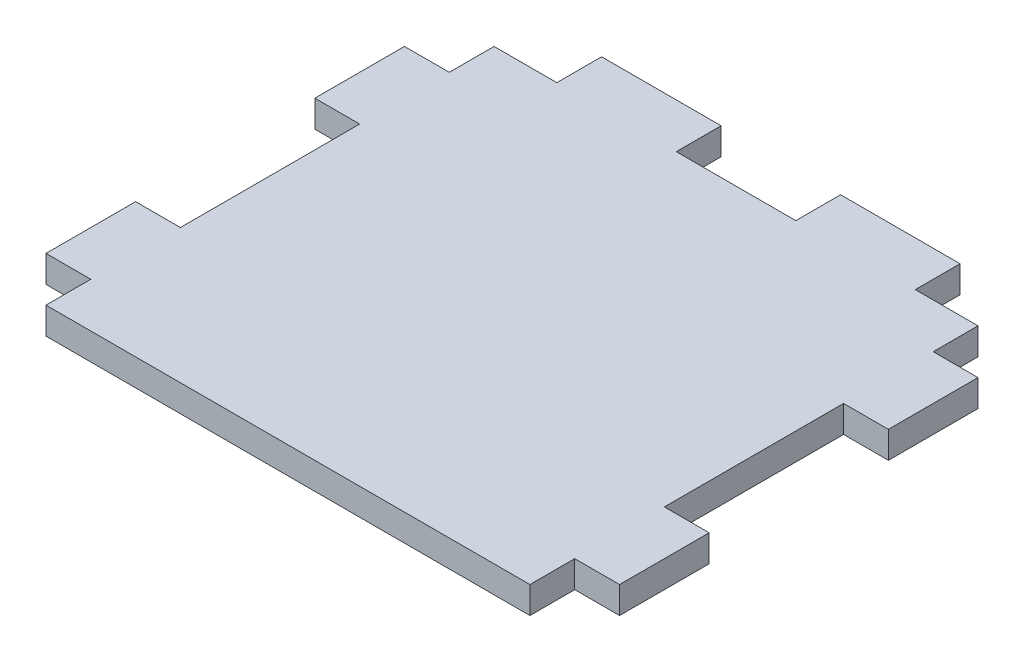
SolidWorks part; units mm, degrees
ref_plane "Front Plane" through (0, 0, 0) normal (0, 0, 1) x (1, 0, 0)
ref_plane "Top Plane" through (0, 0, 0) normal (0, 1, 0) x (1, 0, 0)
ref_plane "Right Plane" through (0, 0, 0) normal (1, 0, 0) x (0, 0, -1)
sketch "Sketch1" plane through (0, 0, 0) normal (0, 1, 0) x (1, 0, 0)
  line L0 (-45, 37.5) -> (-40.5, 37.5)
  line L1 (-45, 37.5) -> (-30, 37.5)
  line L3 (-45, -37.5) -> (45, -37.5)
  line L5 (-45, 37.5) -> (45, -37.5) construction
  line L6 (-45, -37.5) -> (45, 37.5) construction
  line L7 (45, 37.5) -> (40.5, 37.5)
  line L8 (-40.5, 37.5) -> (-40.5, 30)
  line L9 (-45, 37.5) -> (-30, 37.5)
  line L14 (-48, 30) -> (-40.5, 30)
  line L15 (-48, 30) -> (-48, 15)
  line L16 (-48, 15) -> (-40.5, 15)
  line L18 (-48, -30) -> (-48, -15)
  line L19 (-48, -30) -> (-40.5, -30)
  line L21 (-48, -15) -> (-40.5, -15)
  line L23 (48, 15) -> (40.5, 15)
  line L25 (48, 30) -> (40.5, 30)
  line L26 (48, 30) -> (48, 15)
  line L27 (48, -30) -> (40.5, -30)
  line L29 (48, -15) -> (40.5, -15)
  line L30 (48, -30) -> (48, -15)
  line L31 (-40.5, -30) -> (-40.5, -37.5)
  line L32 (40.5, 37.5) -> (40.5, 30)
  line L33 (-40.5, 15) -> (-40.5, -15)
  line L34 (40.5, 15) -> (40.5, -15)
  line L35 (-30, 45) -> (-10, 45)
  line L36 (40.5, -30) -> (40.5, -37.5)
  line L37 (-30, 45) -> (-30, 37.5)
  line L39 (-10, 45) -> (-10, 37.5)
  line L41 (10, 45) -> (10, 37.5)
  line L42 (30, 45) -> (10, 45)
  line L43 (30, 45) -> (30, 37.5)
  line L44 (-10, 37.5) -> (10, 37.5)
  line L45 (30, 37.5) -> (45, 37.5)
  point P0 (0, 0)
  dimension "D1" = 75
  dimension "D2" = 90
  dimension "D3" = 4.5
  dimension "D4" = 4.5
  dimension "D5" = 15
  dimension "D6" = 7.5
  dimension "D7" = 7.5
  dimension "D8" = 7.5
  dimension "D10" = 20
  dimension "D11" = 7.5
extrude "Boss-Extrude1" add sketch "Sketch1" along normal blind 4.5 contours L45 L43 L42 L41 L44 L39 L35 L37 L1 L8 L14 L15 L16 L33 L21 L18 L19 L31 L3 L36 L27 L30 L29 L34 L23 L26 L25 L32
